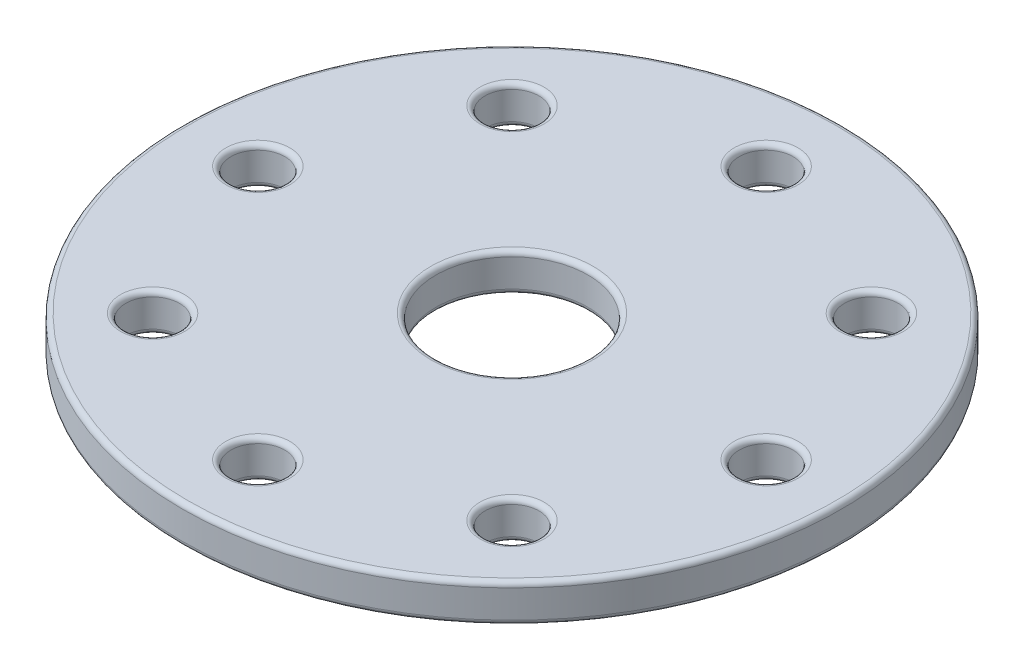
SolidWorks part; units mm, degrees
ref_plane "Front Plane" through (0, 0, 0) normal (0, 0, 1) x (1, 0, 0)
ref_plane "Top Plane" through (0, 0, 0) normal (0, 1, 0) x (1, 0, 0)
ref_plane "Right Plane" through (0, 0, 0) normal (1, 0, 0) x (0, 0, -1)
sketch "Sketch2" plane through (0, 0, 0) normal (0, 1, 0) x (1, 0, 0)
  circle A0 centre (0, 0) radius 32.5
  dimension "D1" = 65
extrude "Boss-Extrude1" add sketch "Sketch2" along normal mid plane 3.75
sketch "Sketch3" plane through (0, 0, 0) normal (0, 1, 0) x (1, 0, 0)
  circle A0 centre (0, 0) radius 7.5
  dimension "D1" = 15
extrude "Cut-Extrude1" cut sketch "Sketch3" against normal through all both and the other way through all
sketch "Sketch4" plane through (0, 0, 0) normal (0, 1, 0) x (1, 0, 0)
  line L0 (0, 32.5) -> (0, 19.875) construction
  line L1 (0, 26.1875) -> (0, 25.0625) construction
  circle A0 centre (0, 25.0625) radius 2.6562
  circle A1 centre (0, 0) radius 19.875 construction
  circle A2 centre (0, 0) radius 32.5 construction
  dimension "D2" = 5.3125
  dimension "D1" = 39.75
  dimension "D3" = 1.125
extrude "Cut-Extrude2" cut sketch "Sketch4" against normal through all both and the other way through all
pattern_circular "CirPattern1" count 8 over 360 about axis through (0, 0, 0) along (0, 1, 0) of "Cut-Extrude2"
fillet "Fillet1" radius 0.5 20 edges at (0, -1.875, 32.5) (0, -1.875, 7.5) (0, -1.875, -22.4063) (-15.8436, -1.875, -15.8436) (15.8436, -1.875, -15.8436) (22.4063, -1.875, 0) (15.8436, -1.875, 15.8436) (0, -1.875, 22.4063) (-15.8436, -1.875, 15.8436) (-22.4063, -1.875, 0) (0, 1.875, 32.5) (0, 1.875, 7.5) (0, 1.875, -22.4063) (-15.8436, 1.875, -15.8436) (15.8436, 1.875, -15.8436) (22.4063, 1.875, 0) (15.8436, 1.875, 15.8436) (0, 1.875, 22.4063) (-15.8436, 1.875, 15.8436) (-22.4063, 1.875, 0)
equation "\"D1@Sketch2\" = \"ARM Static Mount Dia\""
equation "\"D1@Boss-Extrude1\" = \"BODY Seal Thickness\""
equation "\"D1@Sketch3\" = \"ARM Both Wire Hole Dia\""
equation "\"D2@Sketch4\" = \"ARM Static Bolt Size\" + ( \"ALL Bolt Hole Off\" * \"ALL Horz Bolt Hole Off Scalar\" )"
equation "\"D1@CirPattern1\" = \"ARM Static Bolt Count\""
equation "\"D3@Sketch4\" = \"ARM Static Bolt Off\""
equation "\"D1@Sketch4\" = \"ARM Both Dia\""
equation "\"D1@Fillet1\"= \"ALL Small Fillet\""
equation "\"ALL Big Fillet\"= 10.0mm"
equation "\"ALL Medium Fillet\"= 1.0mm"
equation "\"ALL Small Fillet\"= 0.5mm"
equation "\"BODY Rad\"= 82.5mm"
equation "\"BODY End Cut Rad\"= 72.5mm"
equation "\"BODY Height Ext\"= 27.5mm"
equation "\"BODY Bottom Cut Dist\"= 50.0mm"
equation "\"BODY Seal Thickness\"= 3.75mm"
equation "\"BODY Wall Extra Thickness\"= 2.5mm"
equation "\"BODY Bottom Extra Nut Wall\"= 7.5mm"
equation "\"ARM Both Dia\"= 39.75mm"
equation "\"ARM Both Length\"= 67.5mm"
equation "\"ARM Both Wire Hole Dia\"= 15.0mm"
equation "\"ARM Both Prop Seal Thickness\"= 2.5mm"
equation "\"ARM Both Brass Insert Dia\"= 4.875mm"
equation "\"ARM Both Bolt Cut Depth\"= 12.5mm"
equation "\"ARM Both Nema Bolt Off\"= 15.4mm"
equation "\"ARM Both Nema Bolt Depth\"= 2.5mm"
equation "\"ARM Both Nema Width\"= 20.0mm"
equation "\"ARM Both Nema Wall Off\"= 2.5mm"
equation "\"ARM Both Nema Center Dia 1\"= 17.0mm"
equation "\"ARM Both Nema Center Dia 2\"= 10.0mm"
equation "\"ARM Both Nema Bearing OD\"= 16.0mm"
equation "\"ARM Both Nema Bearing ID\"= 10.0mm"
equation "\"ARM Both Nema Bearing Thickness\"= 4.0mm"
equation "\"ARM Both Nema Height\"= 38.0mm"
equation "\"ARM Both Nema Shaft Dia\"= 4.0mm"
equation "\"ARM Both Nema Shaft Length\"= 10.0mm"
equation "\"ARM Both Nema Center Height\"= 1.5mm"
equation "\"ARM Rotating Bearing OD\"= 68.0mm"
equation "\"ARM Rotating Bearing ID\"= 40.0mm"
equation "\"ARM Rotating Bearing Thickness\"= 15.0mm"
equation "\"ARM Static Mount Dia\"= 65.0mm"
equation "\"ARM Static Bolt Off\"= 1.125mm"
equation "\"ALL Bolt Hole Off\"= 0.25mm"
equation "\"ALL Vert Bolt Hole Off Scalar\"= 0.5mm"
equation "\"ALL Horz Bolt Hole Off Scalar\"= 1.25mm"
equation "\"ALL Nut Size Off\"= 0.25mm"
equation "\"ALL Vert Nut Off Scalar\"= 0.5mm"
equation "\"ALL Horz Nut Off Scalar\"= 1.25mm"
equation "\"BODY Bolt Count\"= 12"
equation "\"BODY Bolt Size\"= 6"
equation "\"BODY Bolt Length\"= 22.0mm"
equation "\"BODY Bolt Head Dia\"= IIF ( \"BODY Bolt Size\" = 3 , 5.75mm , IIF ( \"BODY Bolt Size\" = 4 , 7.25mm , IIF ( \"BODY Bolt Size\" = 5 , 8.75mm , IIF ( \"BODY Bolt Size\" = 6 , 10.25mm , 5.75mm ) ) ) )"
equation "\"BODY Bolt Head Height\"= IIF ( \"BODY Bolt Size\" = 3 , 3.0mm , IIF ( \"BODY Bolt Size\" = 4 , 4.0mm , IIF ( \"BODY Bolt Size\" = 5 , 5.0mm , IIF ( \"BODY Bolt Size\" = 6 , 6.0mm , 3.0mm ) ) ) )"
equation "\"BODY Nut Width\"= IIF ( \"BODY Bolt Size\" = 3 , 5.5mm , IIF ( \"BODY Bolt Size\" = 4 , 7.0mm , IIF ( \"BODY Bolt Size\" = 5 , 8.0mm , IIF ( \"BODY Bolt Size\" = 6 , 10.0mm , 5.5mm ) ) ) )"
equation "\"BODY Nut Height\"= IIF ( \"BODY Bolt Size\" = 3 , 4.0mm , IIF ( \"BODY Bolt Size\" = 4 , 5.0mm , IIF ( \"BODY Bolt Size\" = 5 , 5.0mm , IIF ( \"BODY Bolt Size\" = 6 , 6.0mm , 4.0mm ) ) ) )"
equation "\"ARM Static Bolt Count\"= 8"
equation "\"ARM Static Bolt Size\"= 5"
equation "\"ARM Static Bolt Length\"= 20.0mm"
equation "\"ARM Static Bolt Head Dia\"= IIF ( \"ARM Static Bolt Size\" = 3 , 5.75mm , IIF ( \"ARM Static Bolt Size\" = 4 , 7.25mm , IIF ( \"ARM Static Bolt Size\" = 5 , 8.75mm , IIF ( \"ARM Static Bolt Size\" = 6 , 10.25mm , 5.75mm ) ) ) )"
equation "\"ARM Static Bolt Head Height\"= IIF ( \"ARM Static Bolt Size\" = 3 , 3.0mm , IIF ( \"ARM Static Bolt Size\" = 4 , 4.0mm , IIF ( \"ARM Static Bolt Size\" = 5 , 5.0mm , IIF ( \"ARM Static Bolt Size\" = 6 , 6.0mm , 3.0mm ) ) ) )"
equation "\"ARM Static Nut Width\"= IIF ( \"ARM Static Bolt Size\" = 3 , 5.5mm , IIF ( \"ARM Static Bolt Size\" = 4 , 7.0mm , IIF ( \"ARM Static Bolt Size\" = 5 , 8.0mm , IIF ( \"ARM Static Bolt Size\" = 6 , 10.0mm , 5.5mm ) ) ) )"
equation "\"ARM Static Nut Height\"= IIF ( \"ARM Static Bolt Size\" = 3 , 4.0mm , IIF ( \"ARM Static Bolt Size\" = 4 , 5.0mm , IIF ( \"ARM Static Bolt Size\" = 5 , 5.0mm , IIF ( \"ARM Static Bolt Size\" = 6 , 6.0mm , 4.0mm ) ) ) )"
equation "\"ARM Gear Width\"= 10.0mm"
equation "\"ARM Gear Width Off\"= 2.5mm"
equation "\"ARM Gear Bolt Count\"= 4"
equation "\"ARM Gear Rotation\"= 360.0deg"
equation "\"ARM Gear Bolt Size\"= 3"
equation "\"ARM Gear Bolt Length\"= 20.0mm"
equation "\"ARM Gear Bolt Head Dia\"= IIF ( \"ARM Static Bolt Size\" = 3 , 5.75mm , IIF ( \"ARM Static Bolt Size\" = 4 , 7.25mm , IIF ( \"ARM Static Bolt Size\" = 5 , 8.75mm , IIF ( \"ARM Static Bolt Size\" = 6 , 10.25mm , 5.75mm ) ) ) )"
equation "\"ARM Gear Bolt Head Height\"= IIF ( \"ARM Static Bolt Size\" = 3 , 3.0mm , IIF ( \"ARM Static Bolt Size\" = 4 , 4.0mm , IIF ( \"ARM Static Bolt Size\" = 5 , 5.0mm , IIF ( \"ARM Static Bolt Size\" = 6 , 6.0mm , 3.0mm ) ) ) )"
equation "\"ARM Gear Nut Width\"= IIF ( \"ARM Static Bolt Size\" = 3 , 5.5mm , IIF ( \"ARM Static Bolt Size\" = 4 , 7.0mm , IIF ( \"ARM Static Bolt Size\" = 5 , 8.0mm , IIF ( \"ARM Static Bolt Size\" = 6 , 10.0mm , 5.5mm ) ) ) )"
equation "\"ARM Gear Nut Height\"= IIF ( \"ARM Static Bolt Size\" = 3 , 4.0mm , IIF ( \"ARM Static Bolt Size\" = 4 , 5.0mm , IIF ( \"ARM Static Bolt Size\" = 5 , 5.0mm , IIF ( \"ARM Static Bolt Size\" = 6 , 6.0mm , 4.0mm ) ) ) )"
equation "\"ARM Both Prop Plate Bolt Size\"= 3"
equation "\"ARM Both Prop Plate Bolt Length\"= 16.0mm"
equation "\"ARM Both Prop Plate Bolt Head Dia\"= IIF ( \"ARM Both Prop Plate Bolt Size\" = 3 , 5.75mm , IIF ( \"ARM Both Prop Plate Bolt Size\" = 4 , 7.25mm , IIF ( \"ARM Both Prop Plate Bolt Size\" = 5 , 8.75mm , IIF ( \"ARM Both Prop Plate Bolt Size\" = 6 , 10.25mm , 5.75mm ) ) ) )"
equation "\"ARM Both Prop Plate Bolt Head Height\"= IIF ( \"ARM Both Prop Plate Bolt Size\" = 3 , 3.0mm , IIF ( \"ARM Both Prop Plate Bolt Size\" = 4 , 4.0mm , IIF ( \"ARM Both Prop Plate Bolt Size\" = 5 , 5.0mm , IIF ( \"ARM Both Prop Plate Bolt Size\" = 6 , 6.0mm , 3.0mm ) ) ) )"
equation "\"ARM Both Nema Bolt Size\"= 2"
equation "\"ARM Both Nema Bolt Head Dia\"= IIF ( \"ARM Both Nema Bolt Size\" = 3 , 5.75mm , IIF ( \"ARM Both Nema Bolt Size\" = 4 , 7.25mm , IIF ( \"ARM Both Nema Bolt Size\" = 5 , 8.75mm , IIF ( \"ARM Both Nema Bolt Size\" = 6 , 10.25mm , 5.75mm ) ) ) )"
equation "\"ARM Both Nema Bolt Head Height\"= IIF ( \"ARM Both Nema Bolt Size\" = 3 , 3.0mm , IIF ( \"ARM Both Nema Bolt Size\" = 4 , 4.0mm , IIF ( \"ARM Both Nema Bolt Size\" = 5 , 5.0mm , IIF ( \"ARM Both Nema Bolt Size\" = 6 , 6.0mm , 3.0mm ) ) ) )"
